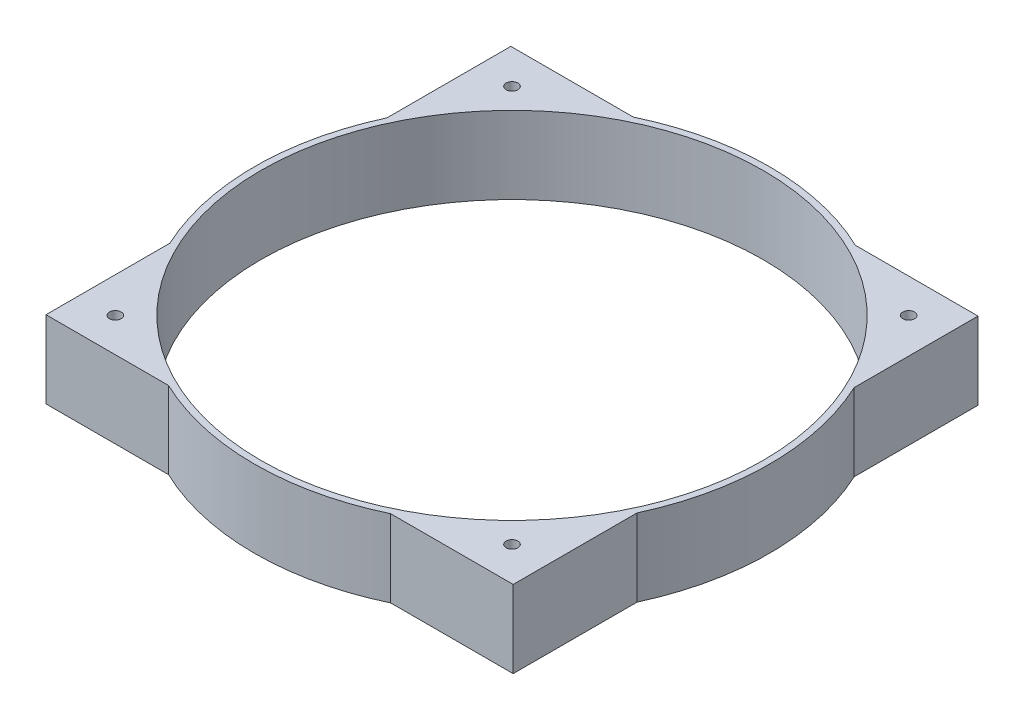
SolidWorks part; units mm, degrees
ref_plane "Front Plane" through (0, 0, 0) normal (0, 0, 1) x (1, 0, 0)
ref_plane "Top Plane" through (0, 0, 0) normal (0, 1, 0) x (1, 0, 0)
ref_plane "Right Plane" through (0, 0, 0) normal (1, 0, 0) x (0, 0, -1)
sketch "Sketch1" plane through (0, 0, 0) normal (0, 1, 0) x (1, 0, 0)
  line L1 (-90.6858, -90.2278) -> (90.6858, -90.2278)
  line L2 (-90.6858, -90.2278) -> (-90.6858, 90.2278)
  line L3 (-90.6858, 90.2278) -> (90.6858, 90.2278)
  line L4 (90.6858, -90.2278) -> (90.6858, 90.2278)
  line L5 (-90.6858, -90.2278) -> (90.6858, 90.2278) construction
  line L6 (-90.6858, 90.2278) -> (90.6858, -90.2278) construction
  circle A0 centre (0, 0) radius 100
  dimension "D1" = 200
extrude "Boss-Extrude1" add sketch "Sketch1" along normal blind 30 contours A0 | L2 L3 L4 L1
sketch "Sketch2" plane through (0, 30, 0) normal (0, 1, 0) x (1, 0, 0)
  line L0 (-77, 77) -> (77, 77) construction
  line L1 (0, 0) -> (0, 77) construction
  line L2 (-77, -77) -> (77, -77) construction
  line L3 (0, 0) -> (0, -77) construction
  circle A0 centre (-77, 77) radius 2.28
  circle A1 centre (77, 77) radius 2.28
  circle A2 centre (-77, -77) radius 2.28
  circle A3 centre (77, -77) radius 2.28
  dimension "D1" = 4.56
  dimension "D2" = 4.56
  dimension "D5" = 4.56
  dimension "D6" = 4.56
  dimension "D3" = 154
  dimension "D4" = 77
extrude "Cut-Extrude1" cut sketch "Sketch2" against normal through all
sketch "Sketch3" plane through (0, 0, 0) normal (0, -1, 0) x (-1, 0, 0)
  circle A0 centre (0, 0) radius 97.5
  dimension "D1" = 195
extrude "Cut-Extrude2" cut sketch "Sketch3" against normal up to surface (30 mm away) up to face at (77, 30, 79.28)
